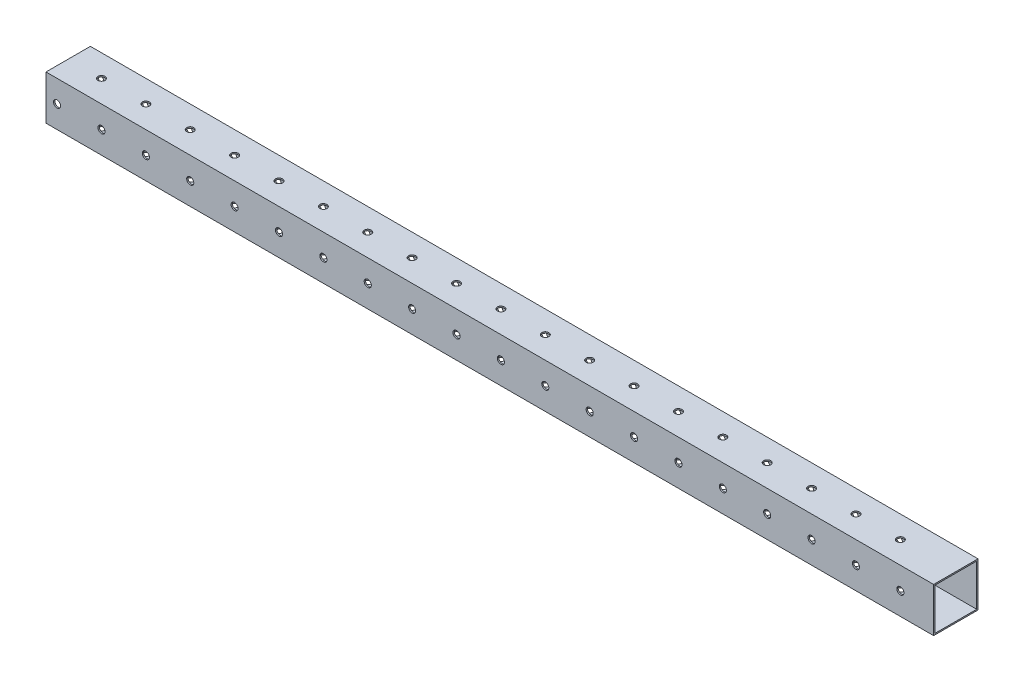
SolidWorks part; units mm, degrees
material "1060 Alloy"
ref_plane "Front Plane" through (0, 0, 0) normal (0, 0, 1) x (1, 0, 0)
ref_plane "Top Plane" through (0, 0, 0) normal (0, 1, 0) x (1, 0, 0)
ref_plane "Right Plane" through (0, 0, 0) normal (1, 0, 0) x (0, 0, -1)
sketch "Sketch1" plane through (0, 0, 0) normal (1, 0, 0) x (0, 0, -1)
  line L1 (0, 0) -> (25.4, 0)
  line L2 (0, 0) -> (0, 25.4)
  line L3 (0, 25.4) -> (25.4, 25.4)
  line L4 (25.4, 0) -> (25.4, 25.4)
  dimension "D1" = 25.4
  dimension "D2" = 25.4
extrude "Extrude-Thin1" add sketch "Sketch1" along normal blind 508 thin thin type one direction reverse wall 0.762
sketch "Sketch2" plane through (0, 0, -25.4) normal (0, 0, -1) x (-1, 0, 0)
  line L0 (0, 0) -> (0, 25.4) construction
  line L1 (-508, 25.4) -> (0, 25.4) construction
  circle A0 centre (-6.35, 12.7) radius 2.032
  circle A1 centre (-31.75, 12.7) radius 2.032
  circle A2 centre (-57.15, 12.7) radius 2.032
  circle A3 centre (-82.55, 12.7) radius 2.032
  circle A4 centre (-107.95, 12.7) radius 2.032
  circle A5 centre (-133.35, 12.7) radius 2.032
  circle A6 centre (-158.75, 12.7) radius 2.032
  circle A7 centre (-184.15, 12.7) radius 2.032
  circle A8 centre (-209.55, 12.7) radius 2.032
  circle A9 centre (-234.95, 12.7) radius 2.032
  circle A10 centre (-260.35, 12.7) radius 2.032
  circle A11 centre (-285.75, 12.7) radius 2.032
  circle A12 centre (-311.15, 12.7) radius 2.032
  circle A13 centre (-336.55, 12.7) radius 2.032
  circle A14 centre (-361.95, 12.7) radius 2.032
  circle A15 centre (-387.35, 12.7) radius 2.032
  circle A16 centre (-412.75, 12.7) radius 2.032
  circle A17 centre (-438.15, 12.7) radius 2.032
  circle A18 centre (-463.55, 12.7) radius 2.032
  circle A19 centre (-488.95, 12.7) radius 2.032
  dimension "D1" = 4.064
  dimension "D2" = 6.35
  dimension "D3" = 12.7
  dimension "D4" = 20
extrude "Cut-Extrude1" cut sketch "Sketch2" against normal through all
sketch "Sketch3" plane through (0, 25.4, 0) normal (0, 1, 0) x (1, 0, 0)
  line L2 (508, 12.7) -> (0, 12.7) construction
  line L5 (508, 25.4) -> (508, 0) construction
  line L6 (0, 25.4) -> (0, 0) construction
  circle A0 centre (476.25, 12.7) radius 2.032
  circle A1 centre (450.85, 12.7) radius 2.032
  circle A2 centre (425.45, 12.7) radius 2.032
  circle A3 centre (400.05, 12.7) radius 2.032
  circle A4 centre (374.65, 12.7) radius 2.032
  circle A5 centre (349.25, 12.7) radius 2.032
  circle A6 centre (323.85, 12.7) radius 2.032
  circle A7 centre (298.45, 12.7) radius 2.032
  circle A8 centre (273.05, 12.7) radius 2.032
  circle A9 centre (247.65, 12.7) radius 2.032
  circle A10 centre (222.25, 12.7) radius 2.032
  circle A11 centre (196.85, 12.7) radius 2.032
  circle A12 centre (171.45, 12.7) radius 2.032
  circle A13 centre (146.05, 12.7) radius 2.032
  circle A14 centre (120.65, 12.7) radius 2.032
  circle A15 centre (95.25, 12.7) radius 2.032
  circle A16 centre (69.85, 12.7) radius 2.032
  circle A17 centre (44.45, 12.7) radius 2.032
  circle A18 centre (19.05, 12.7) radius 2.032
  dimension "D1" = 4.064
  dimension "D2" = 31.75
  dimension "D3" = 19
extrude "Cut-Extrude2" cut sketch "Sketch3" against normal through all
